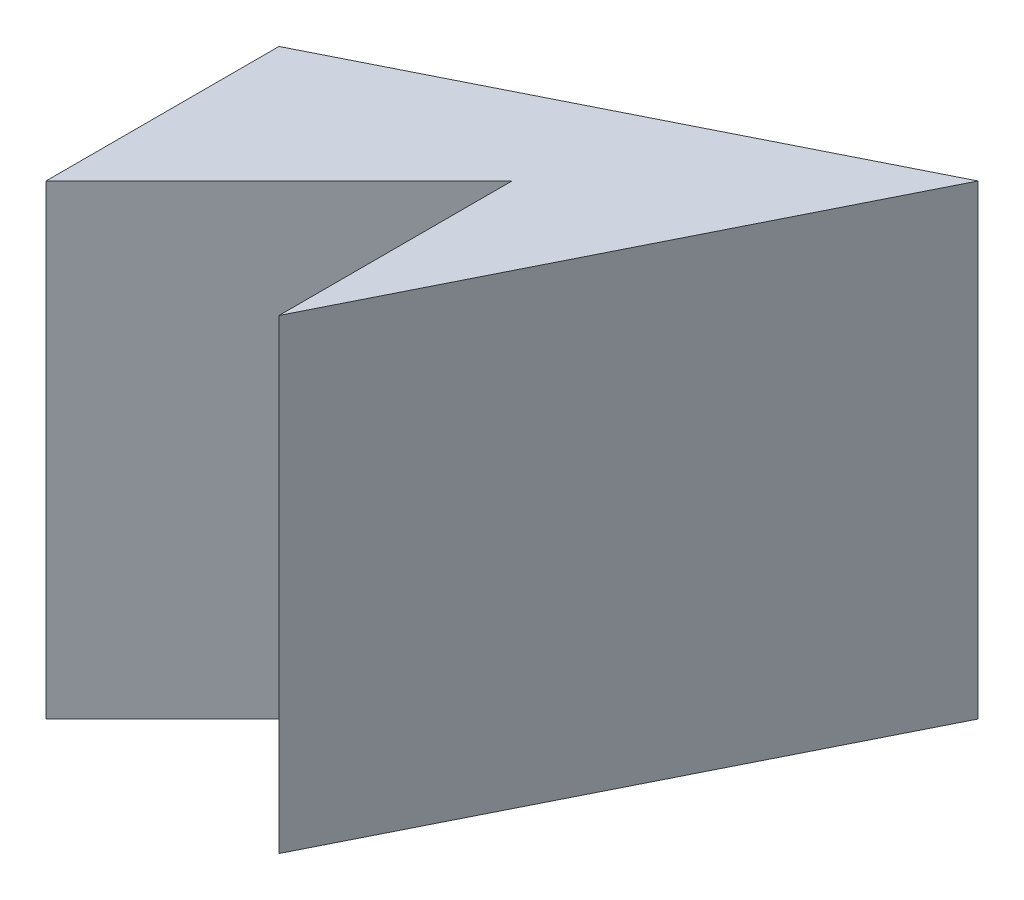
SolidWorks part; units mm, degrees
ref_plane "Front Plane" through (0, 0, 0) normal (0, 0, 1) x (1, 0, 0)
ref_plane "Top Plane" through (0, 0, 0) normal (0, 1, 0) x (1, 0, 0)
ref_plane "Right Plane" through (0, 0, 0) normal (1, 0, 0) x (0, 0, -1)
sketch "Sketch2" plane through (0, 0, 0) normal (0, 1, 0) x (1, 0, 0)
  line L0 (0, 0) -> (0, 2)
  line L1 (0, 2) -> (-2, 0)
  line L2 (-2, 0) -> (-2, 2)
  line L3 (-2, 2) -> (2, 4)
  line L4 (2, 4) -> (0, 0)
  dimension "D1" = 4
  dimension "D2" = 2
  dimension "D3" = 2
  dimension "D4" = 2
  dimension "D5" = 2
  dimension "D6" = 4
extrude "Boss-Extrude2" add sketch "Sketch2" along normal blind 4
